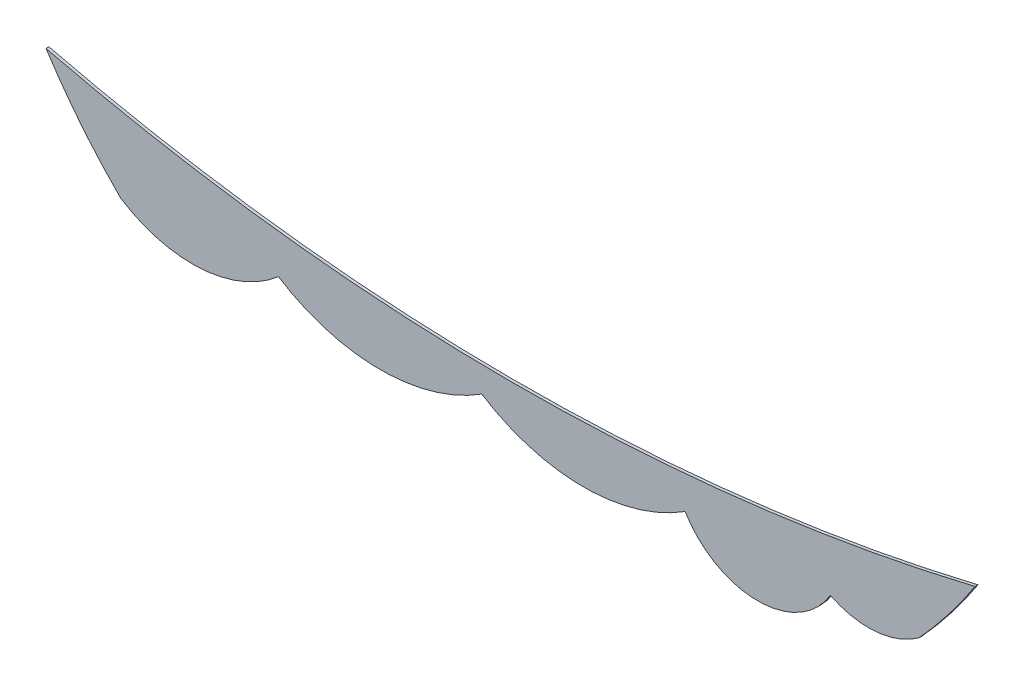
SolidWorks part; units mm, degrees
ref_plane "Alzado" through (0, 0, 0) normal (0, 0, 1) x (1, 0, 0)
ref_plane "Planta" through (0, 0, 0) normal (0, 1, 0) x (1, 0, 0)
ref_plane "Vista lateral" through (0, 0, 0) normal (1, 0, 0) x (0, 0, -1)
sketch "Model" plane through (0, 0, 0) normal (0, 0, 1) x (1, 0, 0)
  arc A0 (21.4764, 16.5883) -> (26.9094, 16.9602) centre (23.945, 20.3963) ccw
  arc A1 (26.9094, 16.9602) -> (33.9094, 16.9602) centre (30.4094, 22.4602) ccw
  arc A2 (33.9094, 16.9602) -> (40.9094, 16.9602) centre (37.4094, 22.4602) ccw
  arc A3 (40.9094, 16.9602) -> (45.9094, 16.9602) centre (43.4094, 18.4602) ccw
  arc A4 (45.9094, 16.9602) -> (48.9637, 17.2233) centre (47.2212, 19.5924) ccw
  arc A5 (18.9094, 19.7648) -> (21.4764, 16.5883) centre (34.9159, 30.0747) ccw
  arc A6 (18.9094, 19.7648) -> (50.8906, 19.7156) centre (35.0017, 85.9009) ccw
  arc A7 (48.9637, 17.2233) -> (50.8906, 19.7156) centre (34.9159, 30.0747) ccw
extrude "Saliente-Extruir1" add sketch "Model" along normal blind 0.1
